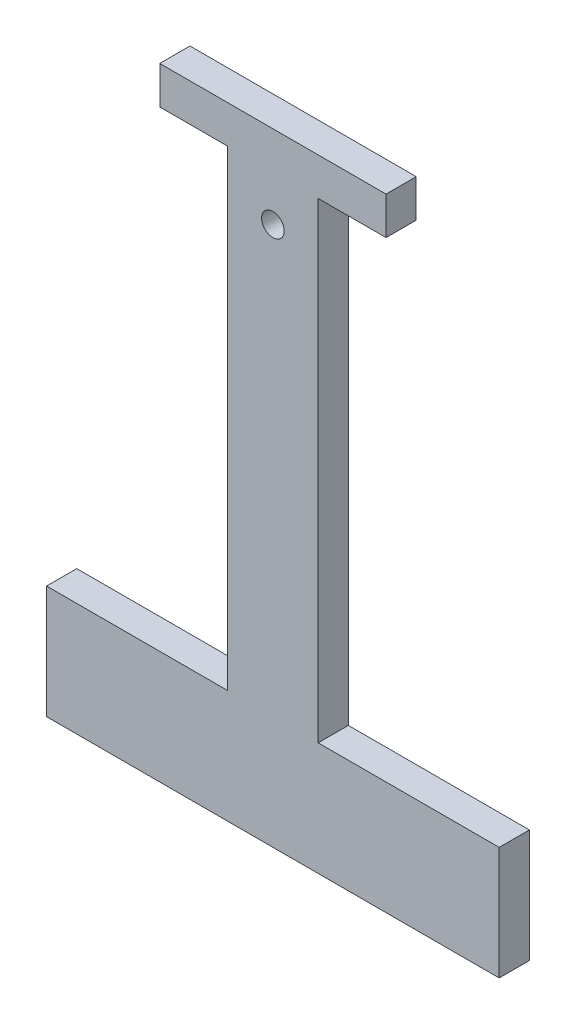
SolidWorks part; units mm, degrees
ref_plane "Спереди" through (0, 0, 0) normal (0, 0, 1) x (1, 0, 0)
ref_plane "Сверху" through (0, 0, 0) normal (0, 1, 0) x (1, 0, 0)
ref_plane "Справа" through (0, 0, 0) normal (1, 0, 0) x (0, 0, -1)
sketch "Эскиз1" plane through (0, 0, 0) normal (0, 0, 1) x (1, 0, 0)
  line L0 (5.7082, 70) -> (14.7082, 70)
  line L5 (-30.2918, -7.5) -> (29.7082, -7.5)
  line L6 (-30.2918, -7.5) -> (-30.2918, 7.5)
  line L7 (-30.2918, 7.5) -> (-6.2918, 7.5)
  line L8 (29.7082, -7.5) -> (29.7082, 7.5)
  line L9 (-15.2918, 70) -> (-6.2918, 70)
  line L10 (-15.2918, 70) -> (-15.2918, 75)
  line L11 (-6.2918, 7.5) -> (-6.2918, 70)
  line L12 (5.7082, 7.5) -> (5.7082, 70)
  line L13 (5.7082, 7.5) -> (29.7082, 7.5)
  line L14 (-15.2918, 75) -> (14.7082, 75)
  line L15 (14.7082, 70) -> (14.7082, 75)
  circle A0 centre (-0.2918, 64) radius 1.5
  point P1 (0, 0)
  point P4 (6, 0)
  dimension "D5" = 3
  dimension "D2" = 5
  dimension "D3" = 60
  dimension "D4" = 15
  dimension "D7" = 30
  dimension "D8" = 9
  dimension "D9" = 9
extrude "Бобышка-Вытянуть1" add sketch "Эскиз1" along normal blind 4
